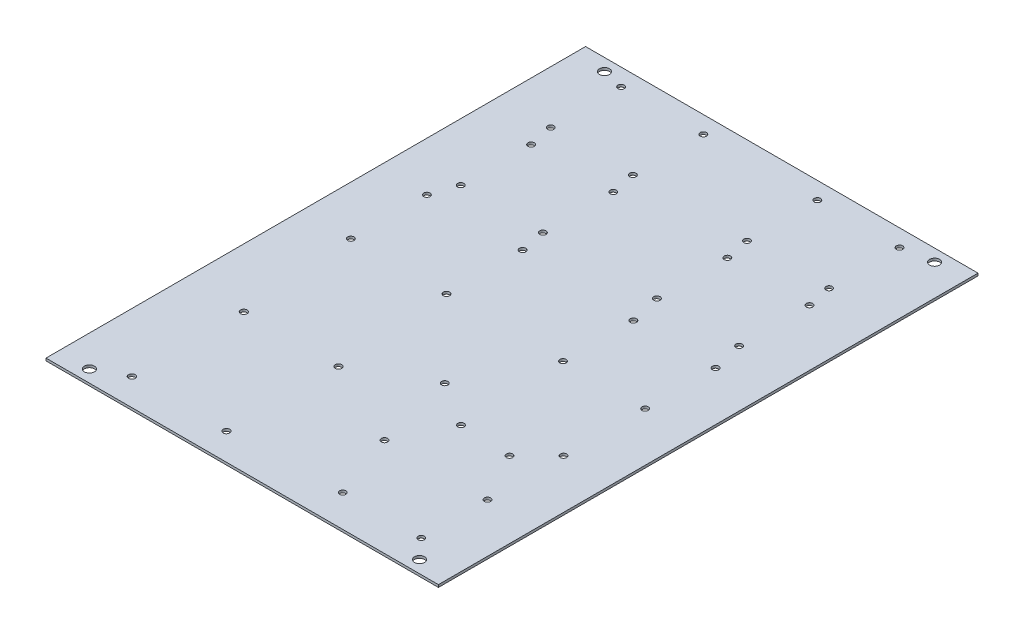
SolidWorks part; units mm, degrees
material "6061-T6 (SS)"
ref_plane "Front Plane" through (0, 0, 0) normal (0, 0, 1) x (1, 0, 0)
ref_plane "Top Plane" through (0, 0, 0) normal (0, 1, 0) x (1, 0, 0)
ref_plane "Right Plane" through (0, 0, 0) normal (1, 0, 0) x (0, 0, -1)
sketch "Sketch1" plane through (0, 0, 0) normal (0, 1, 0) x (1, 0, 0)
  line L1 (-101.6, -139.7) -> (101.6, -139.7)
  line L2 (-101.6, -139.7) -> (-101.6, 139.7)
  line L3 (-101.6, 139.7) -> (101.6, 139.7)
  line L4 (101.6, -139.7) -> (101.6, 139.7)
  line L5 (-101.6, -139.7) -> (101.6, 139.7) construction
  line L6 (-101.6, 139.7) -> (101.6, -139.7) construction
  point P0 (0, 0)
  dimension "D1" = 279.4
  dimension "D2" = 203.2
extrude "Boss-Extrude1" add sketch "Sketch1" along normal blind 1.27
hole_wizard "Mounting Holes" positions "Sketch2" profile "Sketch3" hole size "#6" standard "ANSI Inch" end condition through all
sketch "Sketch2" plane through (0, 1.27, 0) normal (0, 1, 0) x (1, 0, 0)
  line L0 (101.6, 139.7) -> (-101.6, 139.7) construction
  line L1 (-101.6, 139.7) -> (-101.6, -139.7) construction
  line L2 (0, 139.7) -> (0, -139.7) construction
  line L3 (-101.6, -139.7) -> (101.6, -139.7) construction
  line L4 (-101.6, 0) -> (101.6, 0) construction
  line L5 (101.6, -139.7) -> (101.6, 139.7) construction
  point P0 (-85.471, 133.35)
  point P17 (85.471, 133.35)
  point P19 (85.471, -133.35)
  point P20 (-85.471, -133.35)
  dimension "D1" = 85.471
  dimension "D2" = 133.35
sketch "Sketch3" plane through (-85.471, 1.27, -133.35) normal (1, 0, 0) x (0, 0, 1)
  line L0 (0, 0) -> (0, 1.27)
  line L1 (0, 1.27) -> (2.5908, 1.27)
  line L2 (2.5908, 1.27) -> (2.5908, 0)
  line L5 (2.5908, 0) -> (0, 0)
  line L11 (0, -6.35) -> (0, 107.95) construction
  dimension "Thru Hole Dia." = 5.1816
  dimension "Thru Hole Depth" = 1.27
hole_wizard "RoboClaw1" positions "Sketch4" profile "Sketch5" hole size "#4" standard "ANSI Inch" end condition through all
sketch "Sketch4" plane through (0, 1.27, 0) normal (0, 1, 0) x (1, 0, 0)
  line L0 (27.305, 130.81) -> (27.305, 94.361) construction
  line L2 (27.305, 94.361) -> (69.85, 94.361) construction
  line L3 (69.85, 94.361) -> (69.85, 130.81) construction
  line L4 (69.85, 130.81) -> (27.305, 130.81) construction
  line L6 (27.305, 94.361) -> (69.85, 130.81) construction
  line L8 (101.6, 139.7) -> (-101.6, 139.7) construction
  line L9 (101.6, -139.7) -> (101.6, 139.7) construction
  point P0 (69.85, 130.81)
  point P2 (69.85, 94.361)
  point P4 (27.305, 94.361)
  point P6 (27.305, 130.81)
  dimension "D1" = 42.545
  dimension "D2" = 36.449
  dimension "D3" = 8.89
  dimension "D4" = 31.75
sketch "Sketch5" plane through (69.85, 1.27, -130.81) normal (1, 0, 0) x (0, 0, 1)
  line L0 (0, 0) -> (0, 1.27)
  line L1 (0, 1.27) -> (1.6319, 1.27)
  line L2 (1.6319, 1.27) -> (1.6319, 0)
  line L5 (1.6319, 0) -> (0, 0)
  line L11 (0, -6.35) -> (0, 107.95) construction
  dimension "Thru Hole Dia." = 3.2639
  dimension "Thru Hole Depth" = 1.27
pattern_linear "Pattern RC2&3" [suppressed] count 3 spacing 49.149 count 3 spacing 2.54
hole_wizard "RoboClaw4" [suppressed] positions "Sketch6" profile "Sketch7" hole size "#4" standard "ANSI Inch"
sketch "Sketch6" [suppressed] plane through (0, 1.27, 0) normal (0, 1, 0) x (1, 0, 0)
  line L0 (32.385, -84.201) -> (32.385, -120.65) construction
  line L1 (32.385, -120.65) -> (74.93, -120.65) construction
  line L2 (74.93, -120.65) -> (74.93, -84.201) construction
  line L3 (74.93, -84.201) -> (32.385, -84.201) construction
  line L4 (-101.6, -139.7) -> (101.6, -139.7) construction
  circle A4 centre (74.93, 32.512) radius 1.6319
  circle A5 centre (74.93, 32.512) radius 1.6319 construction
  point P0 (32.385, -120.65)
  point P2 (74.93, -120.65)
  point P4 (74.93, -84.201)
  point P6 (32.385, -84.201)
  dimension "D1" = 36.449
  dimension "D2" = 42.545
  dimension "D3" = 19.05
sketch "Sketch7" plane through (32.385, 1.27, 120.65) normal (1, 0, 0) x (0, 0, 1)
  line L0 (0, 0) -> (0, 1.27)
  line L1 (0, 1.27) -> (1.6319, 1.27)
  line L2 (1.6319, 1.27) -> (1.632, 0)
  line L5 (1.632, 0) -> (0, 0)
  line L11 (0, -6.35) -> (0, 107.95) construction
  dimension "Thru Hole Dia." = 3.2639
  dimension "Thru Hole Depth" = 1.27
pattern_linear "Pattern RC5" [suppressed] count 2 spacing 49.149 count 2 spacing 2.54
hole_wizard "Raspberry Pi " positions "Sketch8" profile "Sketch9" hole size "M3" standard "ANSI Metric" end condition through all
sketch "Sketch8" plane through (0, 1.27, 0) normal (0, 1, 0) x (1, 0, 0)
  line L0 (-101.6, 139.7) -> (-101.6, -139.7) construction
  line L1 (-101.6, -139.7) -> (101.6, -139.7) construction
  point P0 (-71.12, -125.73)
  point P2 (-22.1209, -125.73)
  point P4 (-22.1209, -67.7291)
  point P6 (-71.12, -67.7291)
  dimension "D1" = 58.0009
  dimension "D2" = 48.9991
  dimension "D3" = 30.48
  dimension "D4" = 13.97
sketch "Sketch9" plane through (-71.12, 1.27, 125.73) normal (1, 0, 0) x (0, 0, 1)
  line L0 (0, 0) -> (0, 1.27)
  line L1 (0, 1.27) -> (1.7, 1.27)
  line L2 (1.7, 1.27) -> (1.7, 0)
  line L5 (1.7, 0) -> (0, 0)
  line L11 (0, -6.35) -> (0, 107.95) construction
  dimension "Thru Hole Dia." = 3.4
  dimension "Thru Hole Depth" = 1.27
hole_wizard "5V Regulator" [suppressed] positions "Sketch10" profile "Sketch11" hole size "#4" standard "ANSI Inch"
sketch "Sketch10" plane through (0, 1.27, 0) normal (0, 1, 0) x (1, 0, 0)
  line L0 (-57.15, -50.8) -> (-43.18, -50.8) construction
  line L1 (-43.18, -50.8) -> (-43.18, -36.83) construction
  line L2 (-101.6, 139.7) -> (-101.6, -139.7) construction
  line L3 (-101.6, -139.7) -> (101.6, -139.7) construction
  point P0 (-57.15, -50.8)
  point P2 (-43.18, -36.83)
  dimension "D1" = 13.97
  dimension "D2" = 13.97
  dimension "D3" = 44.45
  dimension "D4" = 88.9
sketch "Sketch11" plane through (-57.15, 1.27, 50.8) normal (1, 0, 0) x (0, 0, 1)
  line L0 (0, 0) -> (0, 1.27)
  line L1 (0, 1.27) -> (1.6319, 1.27)
  line L2 (1.6319, 1.27) -> (1.6319, 0)
  line L5 (1.6319, 0) -> (0, 0)
  line L11 (0, -6.35) -> (0, 107.95) construction
  dimension "Thru Hole Dia." = 3.2639
  dimension "Thru Hole Depth" = 1.27
hole_wizard "Buck Boost 1" [suppressed] positions "Sketch12" profile "Sketch13" hole size "#4" standard "ANSI Inch"
sketch "Sketch12" plane through (0, 1.27, 0) normal (0, 1, 0) x (1, 0, 0)
  line L0 (-71.12, 120.65) -> (-17.78, 120.65) construction
  line L1 (-17.78, 120.65) -> (-17.78, 86.36) construction
  line L2 (-17.78, 86.36) -> (-58.42, 86.36) construction
  line L3 (101.6, 139.7) -> (-101.6, 139.7) construction
  line L4 (-101.6, 139.7) -> (-101.6, -139.7) construction
  point P0 (-71.12, 120.65)
  point P2 (-17.78, 120.65)
  point P4 (-17.78, 86.36)
  point P6 (-58.42, 86.36)
  dimension "D1" = 40.64
  dimension "D2" = 53.34
  dimension "D3" = 34.29
  dimension "D4" = 19.05
  dimension "D5" = 30.48
sketch "Sketch13" plane through (-71.12, 1.27, -120.65) normal (1, 0, 0) x (0, 0, 1)
  line L0 (0, 0) -> (0, 1.27)
  line L1 (0, 1.27) -> (1.6319, 1.27)
  line L2 (1.6319, 1.27) -> (1.6319, 0)
  line L5 (1.6319, 0) -> (0, 0)
  line L11 (0, -6.35) -> (0, 107.95) construction
  dimension "Thru Hole Dia." = 3.2639
  dimension "Thru Hole Depth" = 1.27
pattern_linear "BB2&3" [suppressed] count 3 spacing 46.99
pattern_linear "LPattern1" count 2 spacing 49.149 along (0, 0, 1) count 2 spacing 2.54 along (1, 0, 0) skipping (0, 1), (1, 0) of "RoboClaw1"
hole_wizard "#4 Clearance Hole1" positions "Sketch14" profile "Sketch15" hole size "#4" standard "ANSI Inch" end condition up to next
sketch "Sketch14" plane through (0, 1.27, 0) normal (0, 1, 0) x (1, 0, 0)
  line L1 (101.6, 139.7) -> (-101.6, 139.7) construction
  line L2 (101.6, -139.7) -> (101.6, 139.7) construction
  point P0 (33.655, 29.21)
  point P2 (76.2, 29.21)
  point P4 (76.2, -7.239)
  point P6 (33.655, -7.239)
  dimension "D1" = 36.449
  dimension "D2" = 42.545
  dimension "D3" = 110.49
  dimension "D4" = 25.4
sketch "Sketch15" plane through (33.655, 1.27, -29.21) normal (1, 0, 0) x (0, 0, 1)
  line L0 (0, 0) -> (0, 1.27)
  line L1 (0, 1.27) -> (1.6319, 1.27)
  line L2 (1.6319, 1.27) -> (1.6319, 0)
  line L5 (1.6319, 0) -> (0, 0)
  line L11 (0, -6.35) -> (0, 107.95) construction
  dimension "Thru Hole Dia." = 3.2639
  dimension "Thru Hole Depth" = 1.27
hole_wizard "Encoder Board" positions "Sketch16" profile "Sketch17" hole size "#4" standard "ANSI Inch" end condition up to next
sketch "Sketch16" plane through (0, 1.27, 0) normal (0, 1, 0) x (1, 0, 0)
  line L0 (-101.6, 139.7) -> (-101.6, -139.7) construction
  point P0 (-76.2, 32.131)
  point P2 (-26.67, 32.131)
  point P4 (-26.67, -7.239)
  point P6 (-76.2, -7.239)
  point P19 (33.655, -7.239)
  dimension "D1" = 39.37
  dimension "D2" = 49.53
  dimension "D3" = 25.4
sketch "Sketch17" plane through (-76.2, 1.27, -32.131) normal (1, 0, 0) x (0, 0, 1)
  line L0 (0, 0) -> (0, 1.27)
  line L1 (0, 1.27) -> (1.6319, 1.27)
  line L2 (1.6319, 1.27) -> (1.6319, 0)
  line L5 (1.6319, 0) -> (0, 0)
  line L11 (0, -6.35) -> (0, 107.95) construction
  dimension "Thru Hole Dia." = 3.2639
  dimension "Thru Hole Depth" = 1.27
hole_wizard "12V Reg" positions "Sketch18" profile "Sketch19" hole size "#4" standard "ANSI Inch" end condition up to next
sketch "Sketch18" plane through (0, 1.27, 0) normal (0, 1, 0) x (1, 0, 0)
  line L1 (101.6, -139.7) -> (101.6, 139.7) construction
  line L2 (-101.6, -139.7) -> (101.6, -139.7) construction
  point P0 (22.86, -88.9)
  point P2 (76.2, -88.9)
  point P4 (35.56, -123.19)
  point P6 (76.2, -123.19)
  dimension "D1" = 53.34
  dimension "D2" = 34.29
  dimension "D3" = 40.64
  dimension "D4" = 25.4
  dimension "D5" = 16.51
sketch "Sketch19" plane through (22.86, 1.27, 88.9) normal (1, 0, 0) x (0, 0, 1)
  line L0 (0, 0) -> (0, 1.27)
  line L1 (0, 1.27) -> (1.6319, 1.27)
  line L2 (1.6319, 1.27) -> (1.6319, 0)
  line L5 (1.6319, 0) -> (0, 0)
  line L11 (0, -6.35) -> (0, 107.95) construction
  dimension "Thru Hole Dia." = 3.2639
  dimension "Thru Hole Depth" = 1.27
hole_wizard "5V Reg" positions "Sketch20" profile "Sketch21" hole size "#4" standard "ANSI Inch" end condition up to next
sketch "Sketch20" plane through (0, 1.27, 0) normal (0, 1, 0) x (1, 0, 0)
  line L0 (101.6, -139.7) -> (101.6, 139.7) construction
  line L1 (-101.6, -139.7) -> (101.6, -139.7) construction
  point P0 (62.23, -63.5)
  point P2 (76.2, -49.53)
  dimension "D1" = 13.97
  dimension "D2" = 13.97
  dimension "D3" = 25.4
  dimension "D4" = 76.2
sketch "Sketch21" plane through (62.23, 1.27, 63.5) normal (1, 0, 0) x (0, 0, 1)
  line L0 (0, 0) -> (0, 1.27)
  line L1 (0, 1.27) -> (1.6319, 1.27)
  line L2 (1.6319, 1.27) -> (1.6319, 0)
  line L5 (1.6319, 0) -> (0, 0)
  line L11 (0, -6.35) -> (0, 107.95) construction
  dimension "Thru Hole Dia." = 3.2639
  dimension "Thru Hole Depth" = 1.27
pattern_linear "LPattern2" count 2 spacing 101.6 along (-1, 0, 0) of "RoboClaw1"
pattern_linear "LPattern3" count 2 spacing 49.149 along (0, 0, 1) count 2 spacing 2.54 along (1, 0, 0) skipping (0, 1), (1, 0) of "LPattern2"
sketch "Sketch22" plane through (0, 1.27, 0) normal (0, 1, 0) x (1, 0, 0)
  line L1 (10.3731, -45.1762) -> (38.3131, -45.1762) construction
  line L2 (10.3731, -45.1762) -> (10.3731, -64.8612) construction
  line L3 (10.3731, -64.8612) -> (38.3131, -64.8612) construction
  line L4 (38.3131, -45.1762) -> (38.3131, -64.8612) construction
  circle A0 centre (12.9131, -47.7162) radius 1.6319
  circle A1 centre (35.9001, -62.3212) radius 1.6319
  circle A2 centre (62.23, -63.5) radius 1.6319 construction
  dimension "D1" = 2.54
  dimension "D2" = 2.54
  dimension "D3" = 25.527
  dimension "D4" = 2.54
  dimension "D5" = 27.94
  dimension "D6" = 19.685
extrude "Read/Write Board" cut sketch "Sketch22" against normal through all
